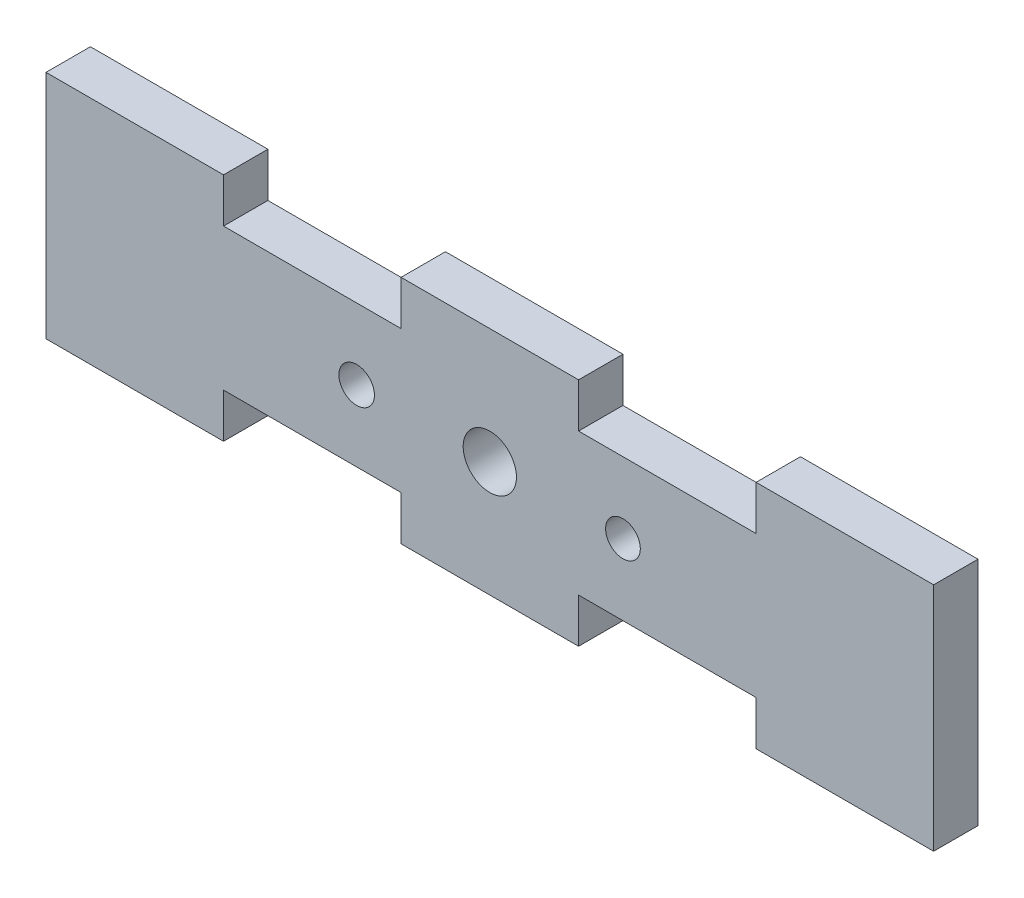
SolidWorks part; units mm, degrees
ref_plane "Alzado" through (0, 0, 0) normal (0, 0, 1) x (1, 0, 0)
ref_plane "Planta" through (0, 0, 0) normal (0, 1, 0) x (1, 0, 0)
ref_plane "Vista lateral" through (0, 0, 0) normal (1, 0, 0) x (0, 0, -1)
sketch "Croquis1" plane through (0, 0, 0) normal (0, 0, 1) x (1, 0, 0)
  line L0 (-25, 6.5) -> (-15, 6.5)
  line L1 (-15, 6.5) -> (-15, 4)
  line L2 (-25, -6.5) -> (-25, 6.5)
  line L3 (-15, 4) -> (-5, 4)
  line L4 (25, -6.5) -> (25, 6.5)
  line L5 (-25, -6.5) -> (25, 6.5) construction
  line L6 (-25, 6.5) -> (25, -6.5) construction
  line L7 (-5, 4) -> (-5, 6.5)
  line L8 (-5, 6.5) -> (5, 6.5)
  line L9 (5, 6.5) -> (5, 4)
  line L10 (5, 4) -> (15, 4)
  line L11 (15, 4) -> (15, 6.5)
  line L12 (15, 6.5) -> (25, 6.5)
  line L13 (-25, -6.5) -> (-15, -6.5)
  line L14 (-15, -6.5) -> (-15, -4)
  line L15 (-15, -4) -> (-5, -4)
  line L16 (-5, -4) -> (-5, -6.5)
  line L17 (-5, -6.5) -> (5, -6.5)
  line L18 (5, -6.5) -> (5, -4)
  line L19 (5, -4) -> (15, -4)
  line L20 (15, -4) -> (15, -6.5)
  line L21 (15, -6.5) -> (25, -6.5)
  circle A0 centre (0, 0) radius 1.5
  circle A1 centre (7.5, 0) radius 0.9778
  circle A2 centre (-7.5, 0) radius 1
  point P0 (0, 0)
  dimension "D1" = 50
  dimension "D2" = 13
extrude "Saliente-Extruir1" add sketch "Croquis1" along normal blind 2.5
